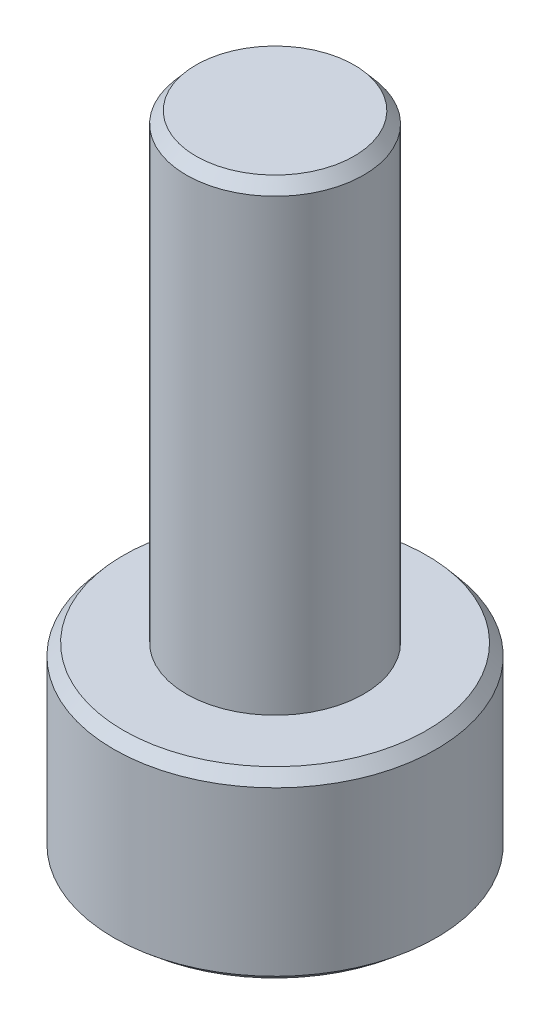
SolidWorks part; units mm, degrees
ref_plane "Front Plane" through (0, 0, 0) normal (0, 0, 1) x (1, 0, 0)
ref_plane "Top Plane" through (0, 0, 0) normal (0, 1, 0) x (1, 0, 0)
ref_plane "Right Plane" through (0, 0, 0) normal (1, 0, 0) x (0, 0, -1)
sketch "Sketch1" plane through (0, 0, 0) normal (0, 1, 0) x (1, 0, 0)
  circle A0 centre (0, 0) radius 3.5
  dimension "D1" = 7
extrude "Boss-Extrude1" add sketch "Sketch1" along normal blind 4
sketch "Sketch2" plane through (0, 4, 0) normal (0, 1, 0) x (1, 0, 0)
  circle A0 centre (0, 0) radius 1.925
  dimension "D1" = 3.85
extrude "Boss-Extrude2" add sketch "Sketch2" along normal blind 10
sketch "Sketch3" plane through (0, 0, 0) normal (0, -1, 0) x (1, 0, 0)
  line L1 (0, 2.3719) -> (-2.0541, 1.186)
  line L2 (-2.0541, 1.186) -> (-2.0541, -1.186)
  line L3 (-2.0541, -1.186) -> (0, -2.3719)
  line L4 (0, -2.3719) -> (2.0541, -1.186)
  line L5 (2.0541, -1.186) -> (2.0541, 1.186)
  line L6 (2.0541, 1.186) -> (0, 2.3719)
  circle A0 centre (0, 0) radius 2.0541 construction
extrude "Cut-Extrude1" cut sketch "Sketch3" against normal blind 2
chamfer "Chamfer1" distance 0.25 angle 40 9 edges at (-2.0541, 0, 0) (-1.0271, 0, -1.7789) (1.0271, 0, -1.7789) (2.0541, 0, 0) (1.0271, 0, 1.7789) (-1.0271, 0, 1.7789) (0, 0, 3.5) (0, 4, 3.5) (0, 14, 1.925)
